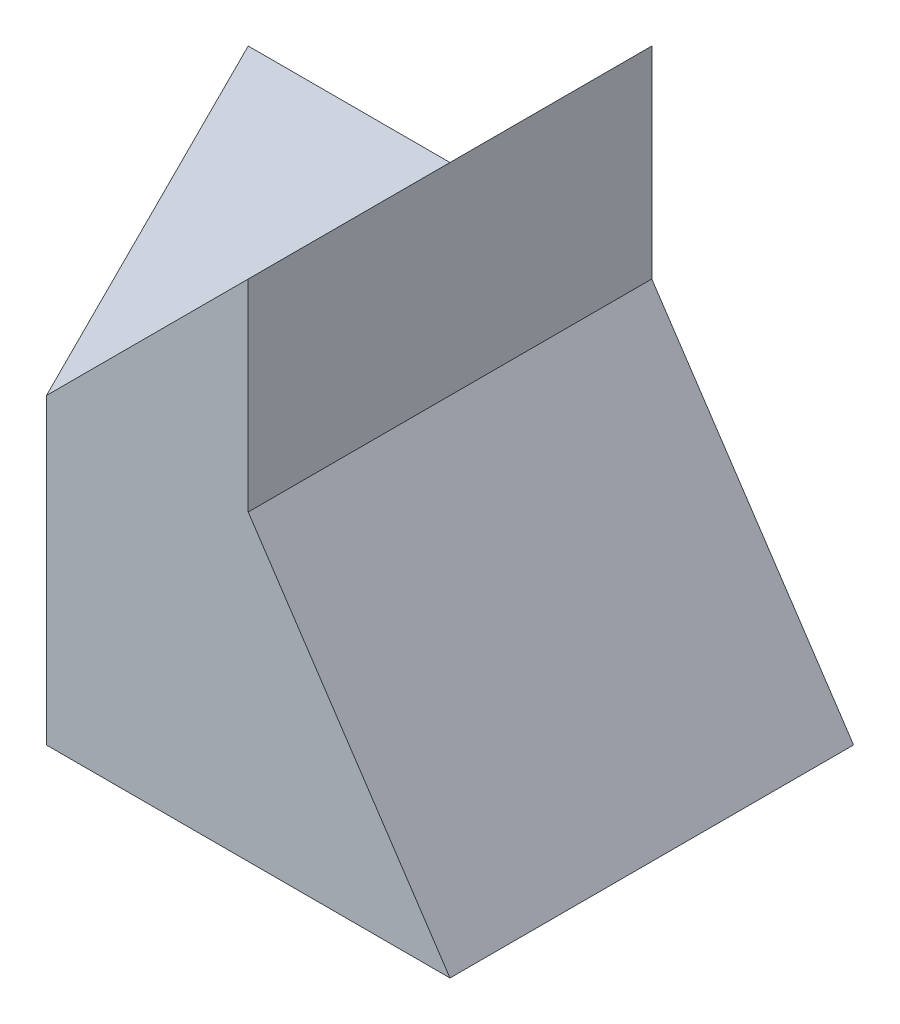
SolidWorks part; units mm, degrees
ref_plane "Front Plane" through (0, 0, 0) normal (0, 0, 1) x (1, 0, 0)
ref_plane "Top Plane" through (0, 0, 0) normal (0, 1, 0) x (1, 0, 0)
ref_plane "Right Plane" through (0, 0, 0) normal (1, 0, 0) x (0, 0, -1)
sketch "Sketch1" plane through (0, 0, 0) normal (0, 1, 0) x (1, 0, 0)
  line L0 (0, 0) -> (-2, 4)
  line L1 (-2, 4) -> (0, 4)
  line L2 (0, 4) -> (0, 0)
  dimension "D1" = 4
  dimension "D2" = 2
extrude "Boss-Extrude1" add sketch "Sketch1" along normal blind 3
sketch "Sketch2" plane through (0, 0, -4) normal (0, 0, -1) x (-1, 0, 0)
  line L0 (0, 3) -> (-2, 5)
  line L1 (-2, 5) -> (-2, 3)
  line L2 (-2, 3) -> (-4, 0)
  line L3 (-4, 0) -> (0, 0)
  line L4 (0, 0) -> (0, 3)
  dimension "D1" = 2
  dimension "D2" = 2
  dimension "D3" = 4
  dimension "D4" = 3
  dimension "D5" = 2
extrude "Boss-Extrude2" add sketch "Sketch2" against normal blind 4
